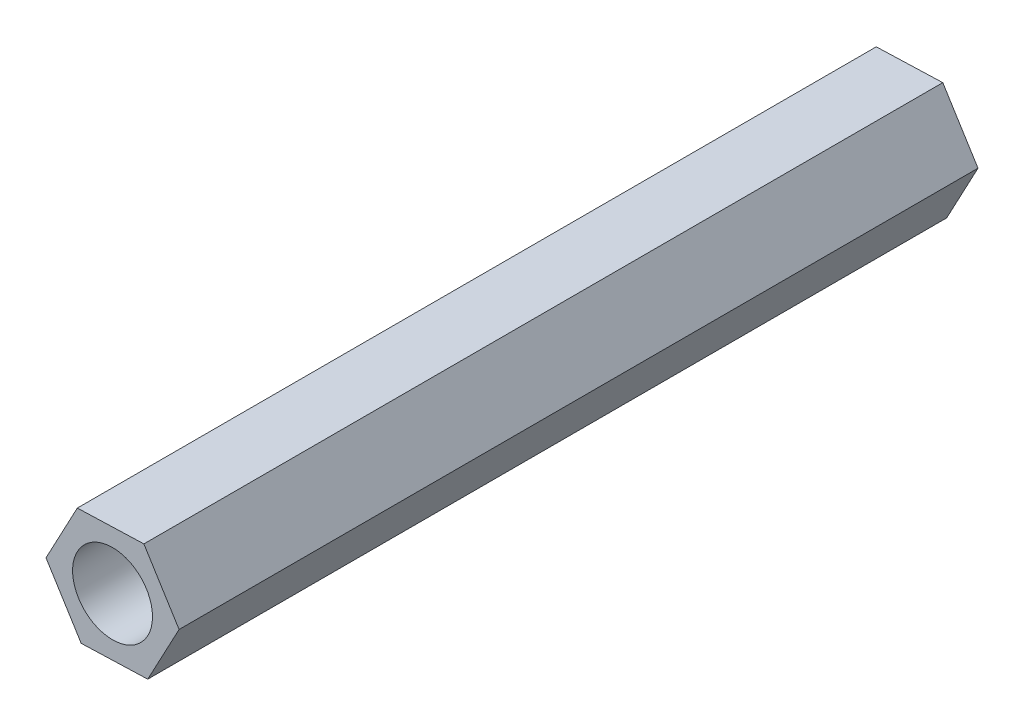
SolidWorks part; units mm, degrees
ref_plane "Front Plane" through (0, 0, 0) normal (0, 0, 1) x (1, 0, 0)
ref_plane "Top Plane" through (0, 0, 0) normal (0, 1, 0) x (1, 0, 0)
ref_plane "Right Plane" through (0, 0, 0) normal (1, 0, 0) x (0, 0, -1)
sketch "Sketch1" plane through (0, 0, 0) normal (0, 0, 1) x (1, 0, 0)
  line L1 (2.6437, -4.2439) -> (4.9972, 0.1676)
  line L2 (4.9972, 0.1676) -> (2.3535, 4.4115)
  line L3 (2.3535, 4.4115) -> (-2.6437, 4.2439)
  line L4 (-2.6437, 4.2439) -> (-4.9972, -0.1676)
  line L5 (-4.9972, -0.1676) -> (-2.3535, -4.4115)
  line L6 (-2.3535, -4.4115) -> (2.6437, -4.2439)
  circle A0 centre (0, 0) radius 4.3301 construction
  circle A1 centre (0, 0) radius 3
  dimension "D2" = 6
  dimension "D1" = 5
extrude "Boss-Extrude1" add sketch "Sketch1" along normal blind 60 contours L1 L2 L3 L4 L5 L6 | A1
